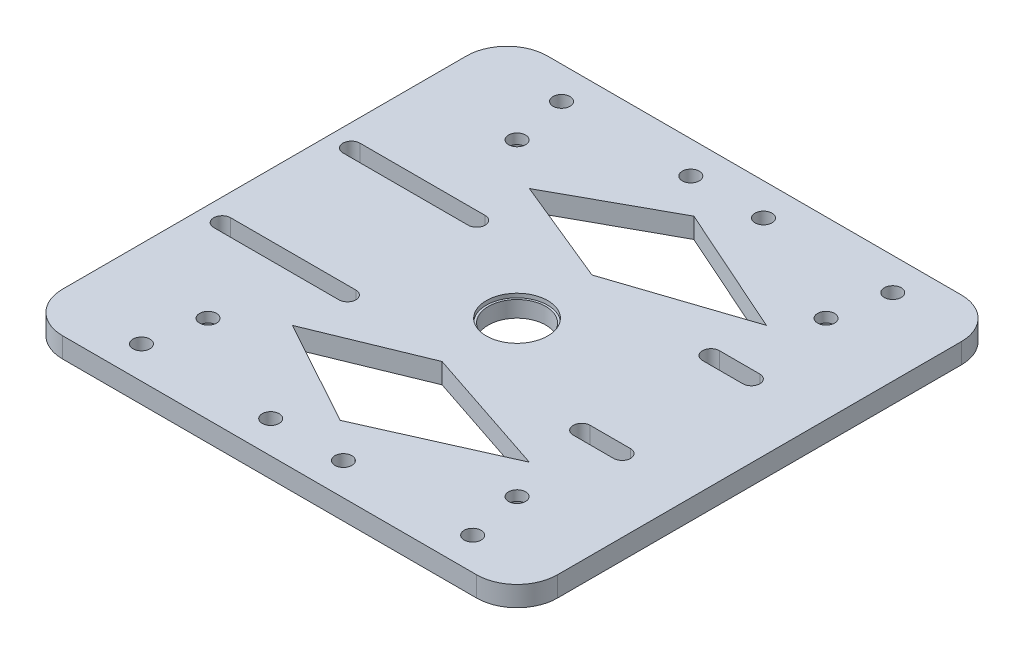
SolidWorks part; units mm, degrees
ref_plane "Front Plane" through (0, 0, 0) normal (0, 0, 1) x (1, 0, 0)
ref_plane "Top Plane" through (0, 0, 0) normal (0, 1, 0) x (1, 0, 0)
ref_plane "Right Plane" through (0, 0, 0) normal (1, 0, 0) x (0, 0, -1)
sketch "Sketch2" plane through (0, 0, 0) normal (0, 1, 0) x (1, 0, 0)
  line L0 (-50, -60) -> (-52.5, -60)
  line L1 (-50, 60) -> (50, 60)
  line L2 (-60, 50) -> (-60, -50)
  line L3 (-50, -60) -> (50, -60)
  line L4 (60, 50) -> (60, -50)
  line L5 (-60, 60) -> (60, -60) construction
  line L6 (-60, -60) -> (60, 60) construction
  line L7 (-38.25, 38.25) -> (38.25, 38.25) construction
  line L8 (-38.25, 38.25) -> (-38.25, -38.25) construction
  line L9 (-38.25, -38.25) -> (38.25, -38.25) construction
  line L10 (38.25, 38.25) -> (38.25, -38.25) construction
  line L11 (-38.25, 38.25) -> (38.25, -38.25) construction
  line L12 (-38.25, -38.25) -> (38.25, 38.25) construction
  line L13 (-50, 60) -> (-52.5, 60)
  line L14 (-62.5, 50) -> (-62.5, -50)
  circle A0 centre (-38.25, 38.25) radius 2.1
  circle A1 centre (38.25, 38.25) radius 2.1
  circle A2 centre (38.25, -38.25) radius 2.1
  circle A3 centre (-38.25, -38.25) radius 2.1
  circle A4 centre (0, 0) radius 7.1
  arc A6 (-60, 50) -> (-50, 60) centre (-50, 50) cw
  arc A7 (60, 50) -> (50, 60) centre (50, 50) ccw
  arc A8 (-50, -60) -> (-60, -50) centre (-50, -50) cw
  arc A9 (60, -50) -> (50, -60) centre (50, -50) cw
  arc A10 (-52.5, 60) -> (-62.5, 50) centre (-52.5, 50) ccw
  arc A11 (-52.5, -60) -> (-62.5, -50) centre (-52.5, -50) cw
  point P0 (0, 0)
  point P6 (0, 0)
  point P35 (-62.5, -60)
  dimension "D5" = 4.2
  dimension "D6" = 14.2
  dimension "D8" = 10
  dimension "D9" = 10
  dimension "D10" = 10
  dimension "D11" = 10
  dimension "D7" = 12.5
  dimension "D12" = 10
  dimension "D13" = 10
  dimension "D1" = 120
  dimension "D2" = 120
  dimension "D3" = 76.5
  dimension "D4" = 76.5
extrude "Boss-Extrude1" add sketch "Sketch2" along normal blind 5
sketch "Sketch3" plane through (0, 5, 0) normal (0, 1, 0) x (1, 0, 0)
  circle A0 centre (0, 0) radius 7.6
  dimension "D1" = 15.2
extrude "Cut-Extrude1" cut sketch "Sketch3" against normal blind 1
sketch "Sketch4" plane through (0, 0, 0) normal (0, -1, 0) x (1, 0, 0)
  line L0 (-24.9888, 60) -> (-24.9888, 52)
  line L1 (-24, 16) -> (24, 16)
  line L2 (-24, 16) -> (-24, -16)
  line L3 (-24, -16) -> (24, -16)
  line L4 (24, 16) -> (24, -16)
  line L5 (-24, 16) -> (24, -16) construction
  line L6 (-24, -16) -> (24, 16) construction
  line L7 (0.0112, 60) -> (0.0112, 43.8657) construction
  line L8 (-40.9888, 52) -> (-8.9888, 52) construction
  line L9 (-46.4888, 52) -> (-3.4888, 52)
  line L10 (-52.5, 60) -> (50, 60) construction
  line L11 (-24.9888, 60) -> (25.0112, 60)
  line L12 (0, 0) -> (77.4554, 0) construction
  circle A0 centre (-40.9888, 52) radius 2.1
  circle A1 centre (-8.9888, 52) radius 2.1
  circle A2 centre (41.0112, 52) radius 2.1
  circle A3 centre (9.0112, 52) radius 2.1
  circle A4 centre (41.0112, -52) radius 2.1
  circle A5 centre (9.0112, -52) radius 2.1
  circle A6 centre (-8.9888, -52) radius 2.1
  circle A7 centre (-40.9888, -52) radius 2.1
  point P0 (0, 0)
  point P13 (-24.9888, 52)
  point P18 (0.0112, 60)
  point P26 (-24.9888, 52)
  dimension "D5" = 4.2
  dimension "D1" = 32
  dimension "D2" = 24
  dimension "D3" = 8
  dimension "D4" = 32
  dimension "D6" = 50
  dimension "D7" = 43
extrude "Cut-Extrude2" cut sketch "Sketch4" against normal through all contours A7 | A6 | A5 | A4 | L9 A0 | L9 A0 | L9 A1 | L9 A1 | A3 | A2
sketch "Sketch5" plane through (0, 0, 0) normal (0, -1, 0) x (1, 0, 0)
  circle A0 centre (-38.25, 38.25) radius 4
  circle A1 centre (38.25, 38.25) radius 4
  circle A2 centre (38.25, -38.25) radius 4
  circle A3 centre (-38.25, -38.25) radius 4
  dimension "D1" = 8
extrude "Cut-Extrude3" cut sketch "Sketch5" against normal blind 2.5
sketch "Sketch7" plane through (0, 0, 0) normal (0, -1, 0) x (1, 0, 0)
  line L0 (0, 0) -> (32, 0) construction
  line L1 (32, 16) -> (32, -16) construction
  line L2 (32, 16) -> (42, 16)
  line L3 (32, 18.1) -> (42, 18.1)
  line L4 (32, 13.9) -> (42, 13.9)
  line L5 (32, -13.9) -> (42, -13.9)
  line L6 (32, -18.1) -> (42, -18.1)
  circle A0 centre (0, 0) radius 18.5 construction
  arc A1 (32, 18.1) -> (32, 13.9) centre (32, 16) ccw
  arc A3 (42, 13.9) -> (42, 18.1) centre (42, 16) ccw
  arc A4 (32, -18.1) -> (32, -13.9) centre (32, -16) cw
  arc A5 (42, -13.9) -> (42, -18.1) centre (42, -16) cw
  point P6 (32, 0)
  dimension "D1" = 32
  dimension "D3" = 4.2
  dimension "D2" = 32
  dimension "D5" = 10
extrude "Cut-Extrude4" cut sketch "Sketch7" against normal through all
sketch "Sketch8" plane through (0, 0, 0) normal (0, -1, 0) x (1, 0, 0)
  line L0 (0, 0) -> (-69, 0)
  line L1 (-57, 16) -> (-57, -16)
  line L3 (-57, 18.1) -> (-26, 18.1)
  line L4 (-57, 13.9) -> (-26, 13.9)
  line L5 (-57, -13.9) -> (-26, -13.9)
  line L6 (-57, -18.1) -> (-26, -18.1)
  arc A1 (-57, 18.1) -> (-57, 13.9) centre (-57, 16) ccw
  arc A2 (-26, 13.9) -> (-26, 18.1) centre (-26, 16) ccw
  arc A3 (-26, -13.9) -> (-26, -18.1) centre (-26, -16) cw
  arc A4 (-57, -18.1) -> (-57, -13.9) centre (-57, -16) cw
  point P7 (-57, 0)
  point P17 (-57, 0)
  dimension "D1" = 57
  dimension "D4" = 4.2
extrude "Cut-Extrude5" cut sketch "Sketch8" against normal through all
sketch "Sketch9" plane through (0, 5, 0) normal (0, 1, 0) x (1, 0, 0)
  line L0 (0, 0) -> (47.5575, 0) construction
  line L6 (0, -18.5542) -> (-26.2936, -29.3394)
  line L7 (-26.2936, -29.3394) -> (0, -43.7805)
  line L8 (0, -43.7805) -> (32.3851, -29.3394)
  line L9 (32.3851, -29.3394) -> (0, -18.5542)
  line L10 (0, 43.7805) -> (32.3851, 29.3394)
  line L11 (-26.2936, 29.3394) -> (0, 43.7805)
  line L12 (0, 18.5542) -> (-26.2936, 29.3394)
  line L13 (32.3851, 29.3394) -> (0, 18.5542)
extrude "Cut-Extrude6" cut sketch "Sketch9" against normal through all both and the other way through all
